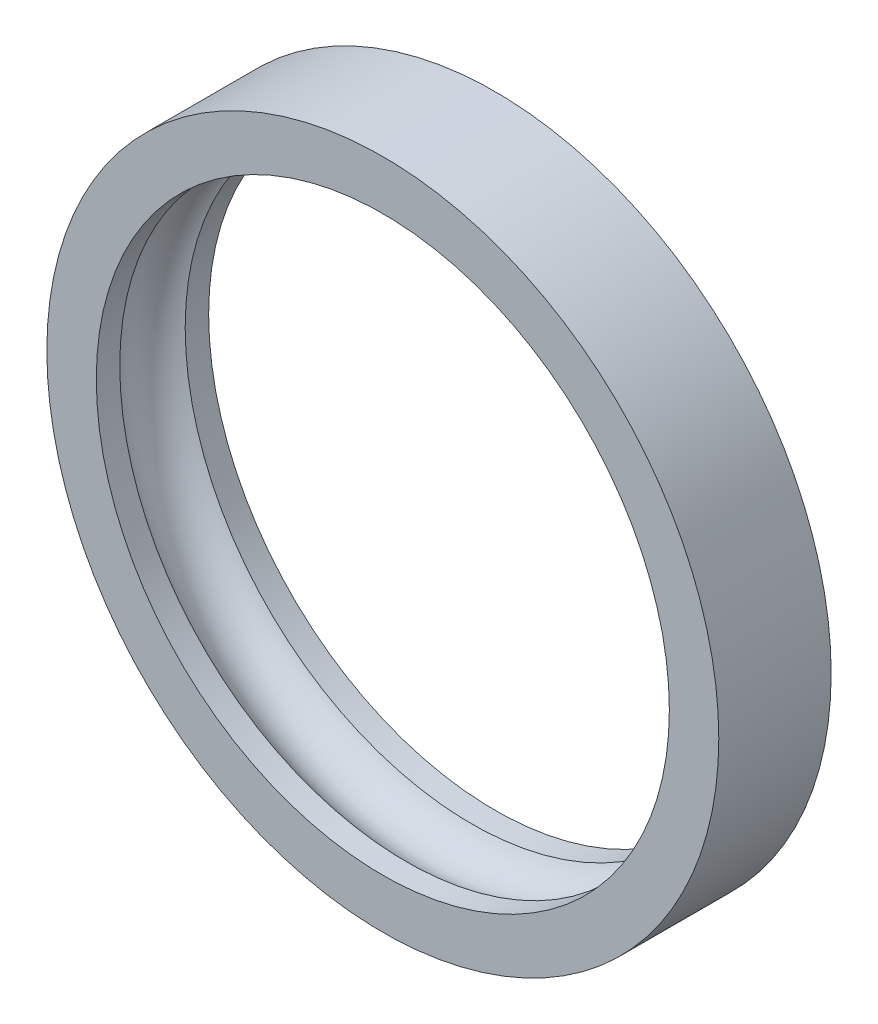
SolidWorks part; units mm, degrees
material "Nylon 101 50%"
ref_plane "Front Plane" through (0, 0, 0) normal (0, 0, 1) x (1, 0, 0)
ref_plane "Top Plane" through (0, 0, 0) normal (0, 1, 0) x (1, 0, 0)
ref_plane "Right Plane" through (0, 0, 0) normal (1, 0, 0) x (0, 0, -1)
ref_axis "Axis1" through (0, 0, -18.4628) along (0, 0, 1)
sketch "Sketch1" plane through (0, 0, 0) normal (0, 0, 1) x (1, 0, 0)
  circle A1 centre (0, 0) radius 29.9 construction
  circle A2 centre (0, 0) radius 29.9
extrude "Boss-Extrude1" add sketch "Sketch1" along normal up to surface (10 mm away)
sketch "Sketch2" plane through (0, 0, 10) normal (0, 0, 1) x (1, 0, 0)
  line L0 (0, 18.1) -> (0, 24) construction
  line L1 (18.1, 0) -> (24, 0) construction
  line L2 (24, 0) -> (29.9, 0) construction
  line L3 (0, 24) -> (0, 25.5) construction
  circle A0 centre (0, 0) radius 25.5
  circle A2 centre (0, 0) radius 18.1 construction
  circle A3 centre (0, 0) radius 18.1 construction
  circle A5 centre (0, 0) radius 24 construction
  circle A6 centre (0, 0) radius 29.9 construction
  dimension "D1" = 1.5
extrude "Cut-Extrude1" cut sketch "Sketch2" against normal up to next
sketch "Sketch3" plane through (0, 0, 0) normal (0, 1, 0) x (1, 0, 0)
  line L0 (-20.825, -5) -> (-20.725, -5) construction
  circle A0 centre (-24, -5) radius 3.175 construction
  circle A1 centre (-24, -5) radius 3.175 construction
  circle A2 centre (-24, -5) radius 3.275
  dimension "D1" = 0.1
revolve "Cut-Revolve2" cut sketch "Sketch3" angle 360 about axis through (0, 0, -18.4628) along (0, 0, 1)
